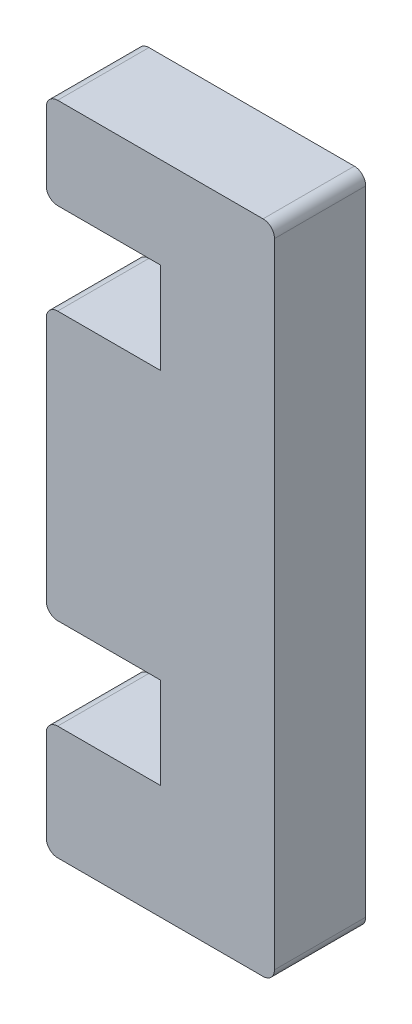
SolidWorks part; units mm, degrees
ref_plane "Front Plane" through (0, 0, 0) normal (0, 0, 1) x (1, 0, 0)
ref_plane "Top Plane" through (0, 0, 0) normal (0, 1, 0) x (1, 0, 0)
ref_plane "Right Plane" through (0, 0, 0) normal (1, 0, 0) x (0, 0, -1)
sketch "Sketch1" plane through (0, 0, 0) normal (0, 0, 1) x (1, 0, 0)
  line L0 (1, 0) -> (19, 0)
  line L1 (20, 1) -> (20, 56.5)
  line L2 (19, 57.5) -> (1, 57.5)
  line L3 (0, 56.5) -> (0, 50.5)
  line L4 (1, 49.5) -> (10, 49.5)
  line L5 (10, 49.5) -> (10, 41.5)
  line L6 (10, 10) -> (1, 10)
  line L7 (0, 9) -> (0, 1)
  line L8 (10, 41.5) -> (1, 41.5)
  line L9 (0, 40.5) -> (0, 19)
  line L10 (1, 18) -> (10, 18)
  line L11 (10, 18) -> (10, 10)
  arc A0 (1, 10) -> (0, 9) centre (1, 9) ccw
  arc A1 (0, 1) -> (1, 0) centre (1, 1) ccw
  arc A2 (19, 0) -> (20, 1) centre (19, 1) ccw
  arc A3 (1, 18) -> (0, 19) centre (1, 19) cw
  arc A4 (0, 40.5) -> (1, 41.5) centre (1, 40.5) cw
  arc A5 (20, 56.5) -> (19, 57.5) centre (19, 56.5) ccw
  arc A6 (1, 57.5) -> (0, 56.5) centre (1, 56.5) ccw
  arc A7 (0, 50.5) -> (1, 49.5) centre (1, 50.5) ccw
  point P13 (5.5, 10)
  point P16 (0, 10)
  point P19 (0, 0)
  point P22 (20, 0)
  dimension "D6" = 1
  dimension "D1" = 10
  dimension "D2" = 8
  dimension "D3" = 20
  dimension "D4" = 10
  dimension "D5" = 31.5
  dimension "D7" = 8
extrude "Boss-Extrude1" add sketch "Sketch1" along normal blind 8
